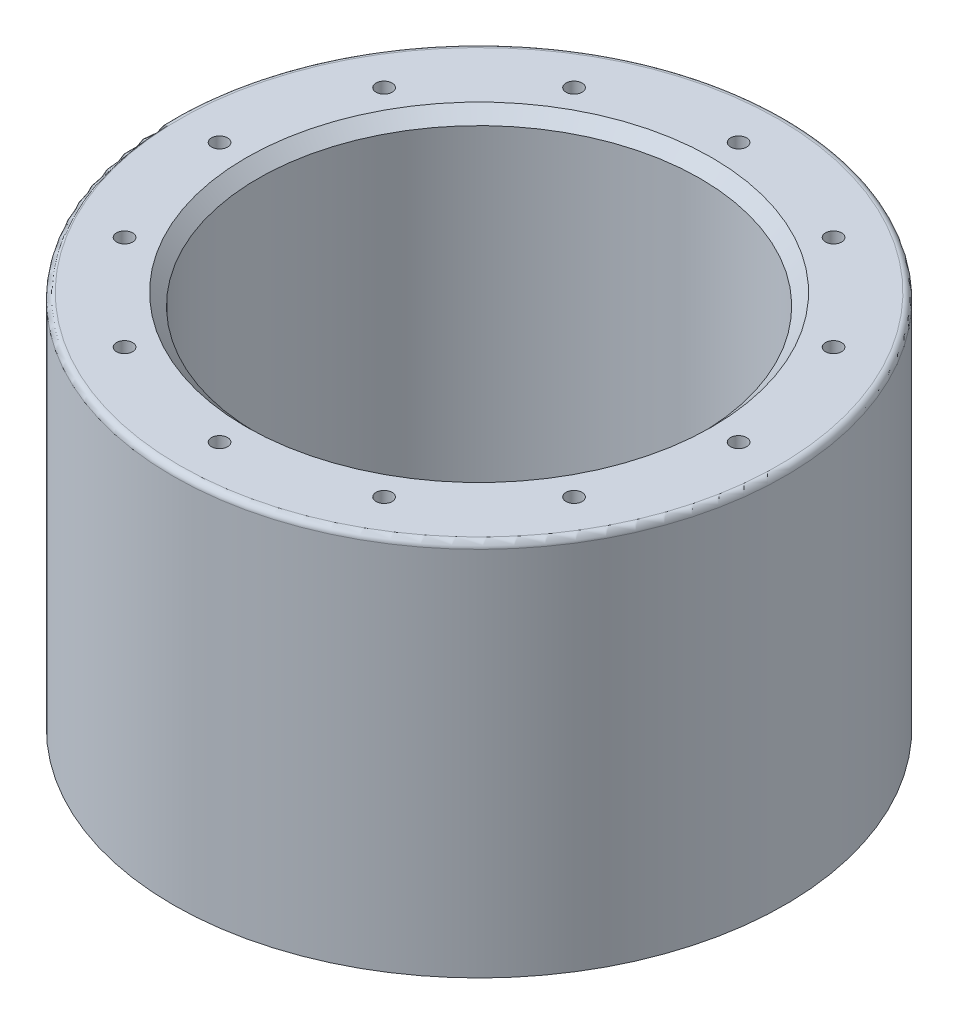
SolidWorks part; units mm, degrees
material "Delrin 2700 NC010, Low Viscosity Acetal Copolymer (SS)"
ref_plane "Front Plane" through (0, 0, 0) normal (0, 0, 1) x (1, 0, 0)
ref_plane "Top Plane" through (0, 0, 0) normal (0, 1, 0) x (1, 0, 0)
ref_plane "Right Plane" through (0, 0, 0) normal (1, 0, 0) x (0, 0, -1)
sketch "Sketch2" plane through (0, 0, 0) normal (0, 1, 0) x (1, 0, 0)
  circle A0 centre (0, 0) radius 97.278
  circle A2 centre (0, 0) radius 70.278
  dimension "D1" = 27
  dimension "D2" = 140.556
extrude "Boss-Extrude2" add sketch "Sketch2" along normal blind 120
sketch "Sketch5" plane through (0, 0, 0) normal (0, -1, 0) x (-1, 0, 0)
  circle A0 centre (0, 0) radius 78.278 construction
  circle A2 centre (0, 78.278) radius 3.175
  circle A3 centre (39.139, 67.7907) radius 3.175
  circle A4 centre (67.7907, 39.139) radius 3.175
  circle A5 centre (78.278, 0) radius 3.175
  circle A6 centre (67.7907, -39.139) radius 3.175
  circle A7 centre (39.139, -67.7907) radius 3.175
  circle A8 centre (0, -78.278) radius 3.175
  circle A9 centre (-39.139, -67.7907) radius 3.175
  circle A10 centre (-67.7907, -39.139) radius 3.175
  circle A11 centre (-78.278, 0) radius 3.175
  circle A12 centre (-67.7907, 39.139) radius 3.175
  circle A13 centre (-39.139, 67.7907) radius 3.175
  circle A14 centre (0, 0) radius 85.4075 construction
  circle A15 centre (0, 0) radius 89.916 construction
  circle A16 centre (0, 0) radius 70.278 construction
  point P32 (0, 0)
  dimension "D1" = 8
  dimension "D2" = 6.35
  dimension "D4" = 170.815
  dimension "D5" = 179.832
  dimension "D3" = 12
sketch "Sketch4" plane through (0, 0, 0) normal (1, 0, 0) x (0, 0, -1)
  line L0 (0, 0) -> (93.091, 0) construction
  line L1 (-97.278, 0) -> (97.278, 0) construction
  line L2 (-97.278, 0) -> (97.278, 0) construction
  line L3 (0, 7.1875) -> (85.471, 7.1875) construction
  line L6 (85.471, 4.2926) -> (93.091, 4.2926)
  line L7 (93.091, 0) -> (93.091, 4.2926)
  line L8 (93.091, 4.2926) -> (93.091, 18.1511) construction
  line L9 (85.471, 4.2926) -> (85.471, 18.0987) construction
  line L10 (85.471, 0) -> (93.091, 0)
  line L11 (0, 0) -> (0, 40.6934) construction
  line L12 (85.471, 0) -> (85.471, 4.2926)
  dimension "D1" = 85.471
  dimension "D2" = 7.62
  dimension "D5" = 4.2926
revolve "Cut-Revolve1" cut sketch "Sketch4" angle 360 about L11
sketch "Sketch6" plane through (0, 120, 0) normal (0, 1, 0) x (1, 0, 0)
  circle A0 centre (0, 0) radius 82.5 construction
  circle A3 centre (0, -82.5) radius 3.175
  circle A4 centre (-41.25, -71.4471) radius 3.175
  circle A5 centre (-71.4471, -41.25) radius 3.175
  circle A6 centre (-82.5, 0) radius 3.175
  circle A7 centre (-71.4471, 41.25) radius 3.175
  circle A8 centre (-41.25, 71.4471) radius 3.175
  circle A9 centre (0, 82.5) radius 3.175
  circle A10 centre (41.25, 71.4471) radius 3.175
  circle A11 centre (71.4471, 41.25) radius 3.175
  circle A12 centre (82.5, 0) radius 3.175
  circle A13 centre (71.4471, -41.25) radius 3.175
  circle A14 centre (41.25, -71.4471) radius 3.175
  point P36 (0, 0)
  dimension "D1" = 6.35
  dimension "D3" = 165
  dimension "D2" = 12
chamfer "Chamfer1" distance 3.8 angle 45 1 edges at (0, 120, 70.278)
hole_wizard "1/4-20 Tapped Hole1" positions "Sketch7" profile "Sketch8" tap size "1/4-20" standard "ANSI Inch"
sketch "Sketch7" plane through (0, 0, 0) normal (0, -1, 0) x (-1, 0, 0)
  point P0 (0, 78.278)
  point P3 (-39.139, 67.7907)
  point P6 (-67.7907, 39.139)
  point P9 (-78.278, 0)
  point P12 (-67.7907, -39.139)
  point P15 (-39.139, -67.7907)
  point P18 (0, -78.278)
  point P21 (39.139, -67.7907)
  point P24 (67.7907, -39.139)
  point P27 (78.278, 0)
  point P30 (67.7907, 39.139)
  point P33 (39.139, 67.7907)
sketch "Sketch8" plane through (0, 0, -78.278) normal (1, 0, 0) x (0, 0, -1)
  line L0 (0, 0) -> (0, 26.9338)
  line L1 (0, 26.9338) -> (2.5527, 25.4)
  line L2 (2.5527, 25.4) -> (2.5527, 0)
  line L5 (2.5527, 0) -> (0, 0)
  line L10 (0, 26.9338) -> (-2.5527, 25.4) construction
  line L11 (0, -6.35) -> (0, 107.95) construction
  dimension "Tap Drill Dia." = 5.1054
  dimension "Tap Drill Depth" = 25.4
  dimension "Drill Angle" = 118
cosmetic thread "Hole Thread1" parameters "D1"=25.4, "D2"=6.35
cosmetic thread "Hole Thread2" parameters "D1"=25.4, "D2"=6.35
cosmetic thread "Hole Thread3" parameters "D1"=25.4, "D2"=6.35
cosmetic thread "Hole Thread4" parameters "D1"=25.4, "D2"=6.35
cosmetic thread "Hole Thread5" parameters "D1"=25.4, "D2"=6.35
cosmetic thread "Hole Thread6" parameters "D1"=25.4, "D2"=6.35
cosmetic thread "Hole Thread7" parameters "D1"=25.4, "D2"=6.35
cosmetic thread "Hole Thread8" parameters "D1"=25.4, "D2"=6.35
cosmetic thread "Hole Thread9" parameters "D1"=25.4, "D2"=6.35
cosmetic thread "Hole Thread10" parameters "D1"=25.4, "D2"=6.35
cosmetic thread "Hole Thread11" parameters "D1"=25.4, "D2"=6.35
cosmetic thread "Hole Thread12" parameters "D1"=25.4, "D2"=6.35
hole_wizard "1/4-20 Tapped Hole2" positions "Sketch9" profile "Sketch10" tap size "1/4-20" standard "ANSI Inch"
sketch "Sketch9" plane through (0, 120, 0) normal (0, 1, 0) x (1, 0, 0)
  point P0 (-41.25, -71.4471)
  point P3 (-71.4471, -41.25)
  point P6 (-82.5, 0)
  point P9 (-71.4471, 41.25)
  point P12 (-41.25, 71.4471)
  point P15 (0, 82.5)
  point P18 (41.25, 71.4471)
  point P21 (71.4471, 41.25)
  point P24 (82.5, 0)
  point P27 (71.4471, -41.25)
  point P30 (41.25, -71.4471)
  point P33 (0, -82.5)
sketch "Sketch10" plane through (-41.25, 120, 71.4471) normal (1, 0, 0) x (0, 0, 1)
  line L0 (0, 0) -> (0, 26.9338)
  line L1 (0, 26.9338) -> (2.5527, 25.4)
  line L2 (2.5527, 25.4) -> (2.5527, 0)
  line L5 (2.5527, 0) -> (0, 0)
  line L10 (0, 26.9338) -> (-2.5527, 25.4) construction
  line L11 (0, -6.35) -> (0, 107.95) construction
  dimension "Tap Drill Dia." = 5.1054
  dimension "Tap Drill Depth" = 25.4
  dimension "Drill Angle" = 118
cosmetic thread "Hole Thread13" parameters "D1"=25.4, "D2"=6.35
cosmetic thread "Hole Thread14" parameters "D1"=25.4, "D2"=6.35
cosmetic thread "Hole Thread15" parameters "D1"=25.4, "D2"=6.35
cosmetic thread "Hole Thread16" parameters "D1"=25.4, "D2"=6.35
cosmetic thread "Hole Thread17" parameters "D1"=25.4, "D2"=6.35
cosmetic thread "Hole Thread18" parameters "D1"=25.4, "D2"=6.35
cosmetic thread "Hole Thread19" parameters "D1"=25.4, "D2"=6.35
cosmetic thread "Hole Thread20" parameters "D1"=25.4, "D2"=6.35
cosmetic thread "Hole Thread21" parameters "D1"=25.4, "D2"=6.35
cosmetic thread "Hole Thread22" parameters "D1"=25.4, "D2"=6.35
cosmetic thread "Hole Thread23" parameters "D1"=25.4, "D2"=6.35
cosmetic thread "Hole Thread24" parameters "D1"=25.4, "D2"=6.35
fillet "Fillet1" radius 2 1 edges at (0, 120, 97.278)
fillet "Fillet2" [suppressed] radius 1
